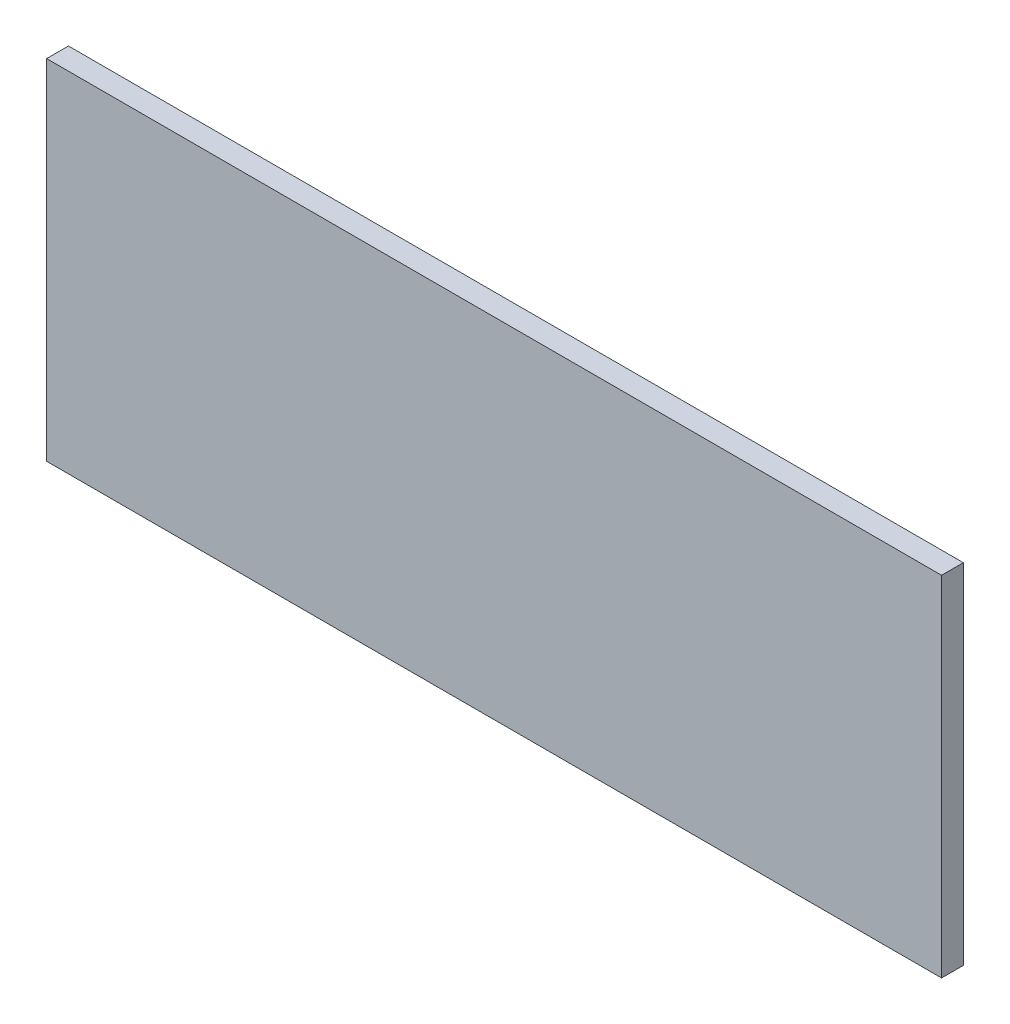
SolidWorks part; units mm, degrees
ref_plane "Front Plane" through (0, 0, 0) normal (0, 0, 1) x (1, 0, 0)
ref_plane "Top Plane" through (0, 0, 0) normal (0, 1, 0) x (1, 0, 0)
ref_plane "Right Plane" through (0, 0, 0) normal (1, 0, 0) x (0, 0, -1)
sketch "Sketch1" plane through (0, 0, 0) normal (0, 0, 1) x (1, 0, 0)
  line L1 (369.5, -144) -> (-369.5, -144)
  line L2 (369.5, -144) -> (369.5, 144)
  line L3 (369.5, 144) -> (-369.5, 144)
  line L4 (-369.5, -144) -> (-369.5, 144)
  line L5 (369.5, -144) -> (-369.5, 144) construction
  line L6 (369.5, 144) -> (-369.5, -144) construction
  point P0 (0, 0)
  dimension "D1" = 288
  dimension "D2" = 739
extrude "Boss-Extrude1" add sketch "Sketch1" along normal blind 18
equation "\"H_DSP\"=18"
equation "\"D1@Boss-Extrude1\"=\"H_DSP\""
